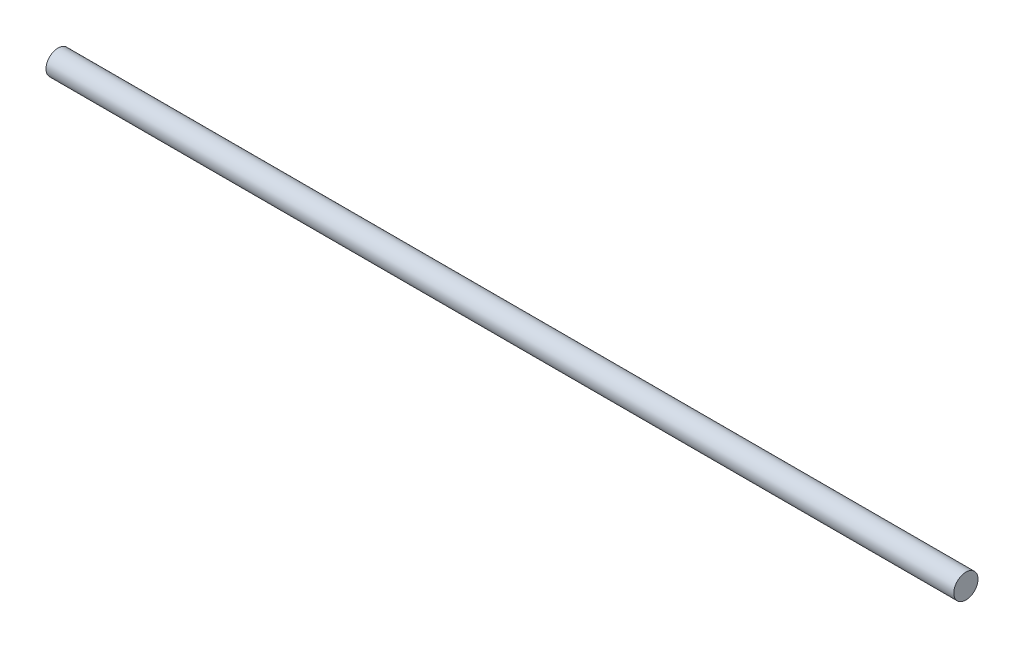
SolidWorks part; units mm, degrees
ref_plane "Front Plane" through (0, 0, 0) normal (0, 0, 1) x (1, 0, 0)
ref_plane "Top Plane" through (0, 0, 0) normal (0, 1, 0) x (1, 0, 0)
ref_plane "Right Plane" through (0, 0, 0) normal (1, 0, 0) x (0, 0, -1)
sketch "Sketch2" plane through (0, 0, 0) normal (1, 0, 0) x (0, 0, -1)
  circle A0 centre (0, 0) radius 4
  dimension "D1" = 8
extrude "Boss-Extrude1" add sketch "Sketch2" along normal blind 300
